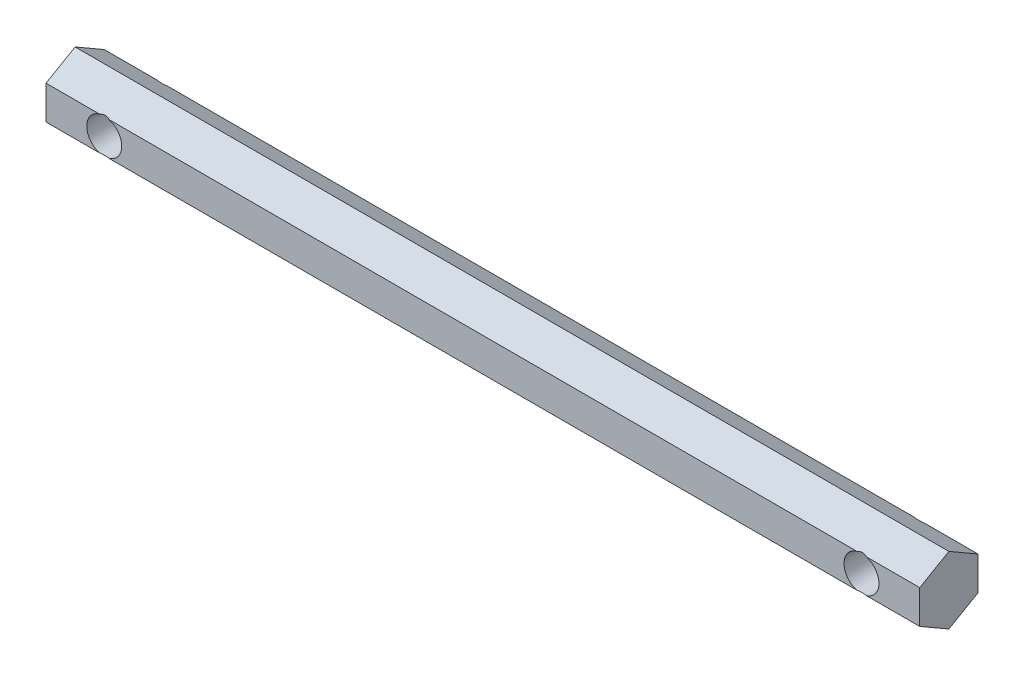
SolidWorks part; units mm, degrees
ref_plane "Plano frontal" through (0, 0, 0) normal (0, 0, 1) x (1, 0, 0)
ref_plane "Plano superior" through (0, 0, 0) normal (0, 1, 0) x (1, 0, 0)
ref_plane "Plano direito" through (0, 0, 0) normal (1, 0, 0) x (0, 0, -1)
sketch "Sketch1" plane through (0, 0, 0) normal (1, 0, 0) x (0, 0, -1)
  line L0 (-8.3414, 2.8868) -> (9.6861, 2.8868) construction
  line L1 (0, 5.7735) -> (-5, 2.8868)
  line L2 (-5, 2.8868) -> (-5, -2.8868)
  line L3 (-5, -2.8868) -> (0, -5.7735)
  line L4 (0, -5.7735) -> (5, -2.8868)
  line L5 (5, -2.8868) -> (5, 2.8868)
  line L6 (5, 2.8868) -> (0, 5.7735)
  line L7 (-8.3414, -2.8868) -> (9.6861, -2.8868) construction
  circle A0 centre (0, 0) radius 5 construction
  dimension "D1" = 10
extrude "Boss-Extrude1" add sketch "Sketch1" along normal mid plane 150
sketch "Sketch2" plane through (0, 0, 0) normal (0, 0, 1) x (1, 0, 0)
  line L0 (120.1463, 0) -> (-122.4896, 0) construction
  line L1 (0, 39.7277) -> (0, -43.0342) construction
  circle A0 centre (65, 0) radius 3
  circle A1 centre (-65, 0) radius 3
  dimension "D3" = 6
  dimension "D4" = 6
  dimension "D1" = 65
  dimension "D2" = 65
extrude "Cut-Extrude1" cut sketch "Sketch2" against normal through all both and the other way through all
